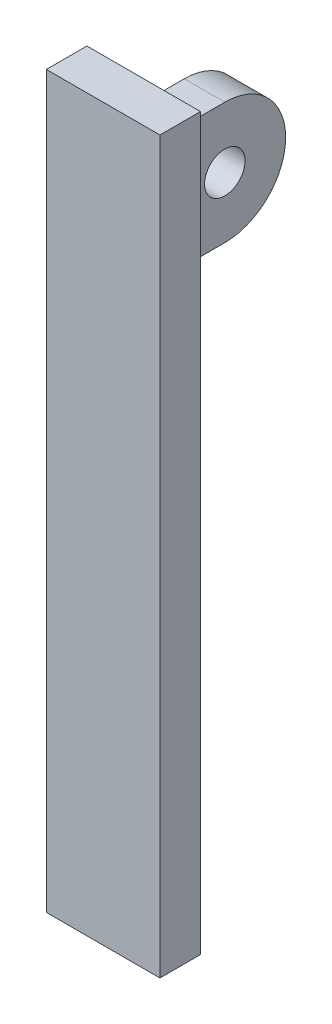
SolidWorks part; units mm, degrees
ref_plane "Front Plane" through (0, 0, 0) normal (0, 0, 1) x (1, 0, 0)
ref_plane "Top Plane" through (0, 0, 0) normal (0, 1, 0) x (1, 0, 0)
ref_plane "Right Plane" through (0, 0, 0) normal (1, 0, 0) x (0, 0, -1)
sketch "Sketch1" plane through (0, 0, 0) normal (0, 1, 0) x (1, 0, 0)
  line L1 (-14, -5) -> (14, -5)
  line L2 (-14, -5) -> (-14, 5)
  line L3 (-14, 5) -> (14, 5)
  line L4 (14, -5) -> (14, 5)
  line L5 (-14, -5) -> (14, 5) construction
  line L6 (-14, 5) -> (14, -5) construction
  point P0 (0, 0)
  dimension "D1" = 10
  dimension "D2" = 28
extrude "Boss-Extrude1" add sketch "Sketch1" along normal blind 270
sketch "Sketch2" plane through (0, 0, -5) normal (0, 0, -1) x (-1, 0, 0)
  line L0 (0, 270) -> (0, 0) construction
  line L1 (-14, 270) -> (14, 270) construction
  line L2 (-14, 0) -> (14, 0) construction
  line L4 (5, 170) -> (-5, 170)
  line L5 (5, 170) -> (5, 140)
  line L6 (5, 140) -> (-5, 140)
  line L7 (-5, 170) -> (-5, 140)
  line L8 (5, 170) -> (-5, 140) construction
  line L9 (5, 140) -> (-5, 170) construction
  point P6 (0, 155)
  dimension "D1" = 140
  dimension "D2" = 30
  dimension "D3" = 10
extrude "Boss-Extrude2" add sketch "Sketch2" along normal blind 30
sketch "Sketch3" plane through (-5, 0, 0) normal (-1, 0, 0) x (0, 0, 1)
  line L0 (-35, 155) -> (-5, 155) construction
  line L1 (-35, 140) -> (-35, 170) construction
  line L2 (-5, 140) -> (-5, 170) construction
  line L3 (-20, 140) -> (-48.5016, 140)
  line L4 (-48.5016, 140) -> (-48.5016, 172.3135)
  line L5 (-48.5016, 172.3135) -> (-20, 170)
  circle A0 centre (-20, 155) radius 5
  arc A1 (-20, 170) -> (-20, 140) centre (-20, 155) ccw
  dimension "D1" = 10
extrude "Cut-Extrude1" cut sketch "Sketch3" against normal blind 30
sketch "Sketch4" plane through (0, 0, -5) normal (0, 0, -1) x (-1, 0, 0)
  line L0 (14, 270) -> (14, 0) construction
  line L1 (-14, 270) -> (14, 270)
  line L2 (-14, 270) -> (-14, 180)
  line L3 (-14, 180) -> (14, 180)
  line L4 (14, 270) -> (14, 180)
  dimension "D1" = 90
extrude "Cut-Extrude2" cut sketch "Sketch4" against normal blind 10
